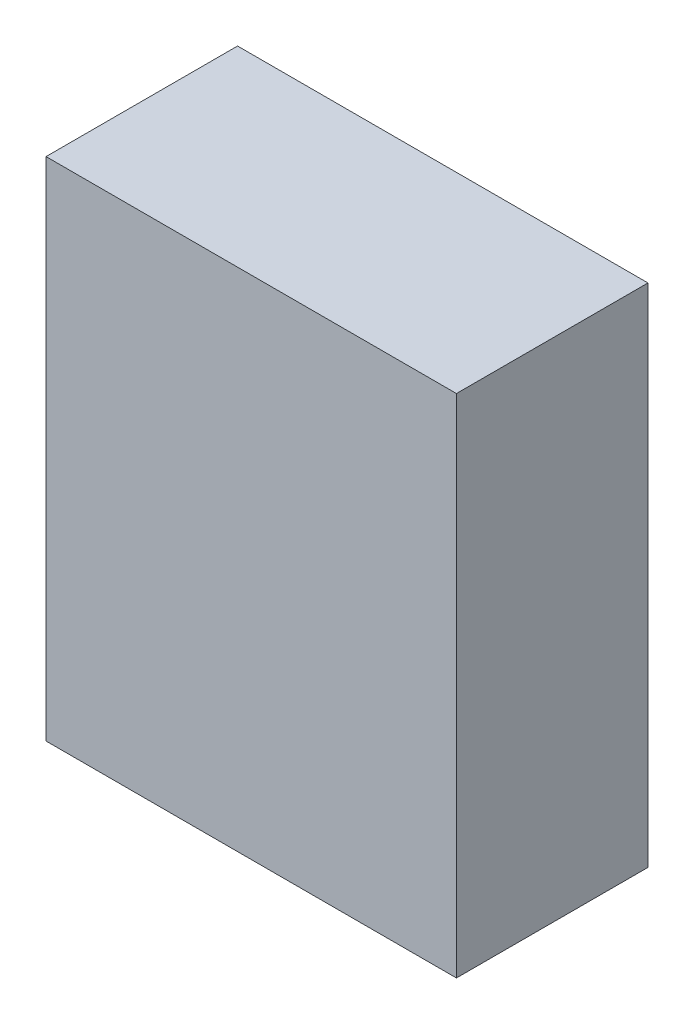
SolidWorks part; units mm, degrees
ref_plane "Front Plane" through (0, 0, 0) normal (0, 0, 1) x (1, 0, 0)
ref_plane "Top Plane" through (0, 0, 0) normal (0, 1, 0) x (1, 0, 0)
ref_plane "Right Plane" through (0, 0, 0) normal (1, 0, 0) x (0, 0, -1)
sketch "Sketch1" plane through (0, 0, 0) normal (0, 0, 1) x (1, 0, 0)
  line L1 (-23.8125, -29.3688) -> (23.8125, -29.3688)
  line L2 (-23.8125, -29.3688) -> (-23.8125, 29.3687)
  line L3 (-23.8125, 29.3687) -> (23.8125, 29.3687)
  line L4 (23.8125, -29.3688) -> (23.8125, 29.3687)
  line L5 (-23.8125, -29.3688) -> (23.8125, 29.3687) construction
  line L6 (-23.8125, 29.3687) -> (23.8125, -29.3688) construction
  point P0 (0, 0)
  dimension "D1" = 58.7375
  dimension "D2" = 47.625
extrude "Boss-Extrude1" add sketch "Sketch1" along normal blind 22.225
